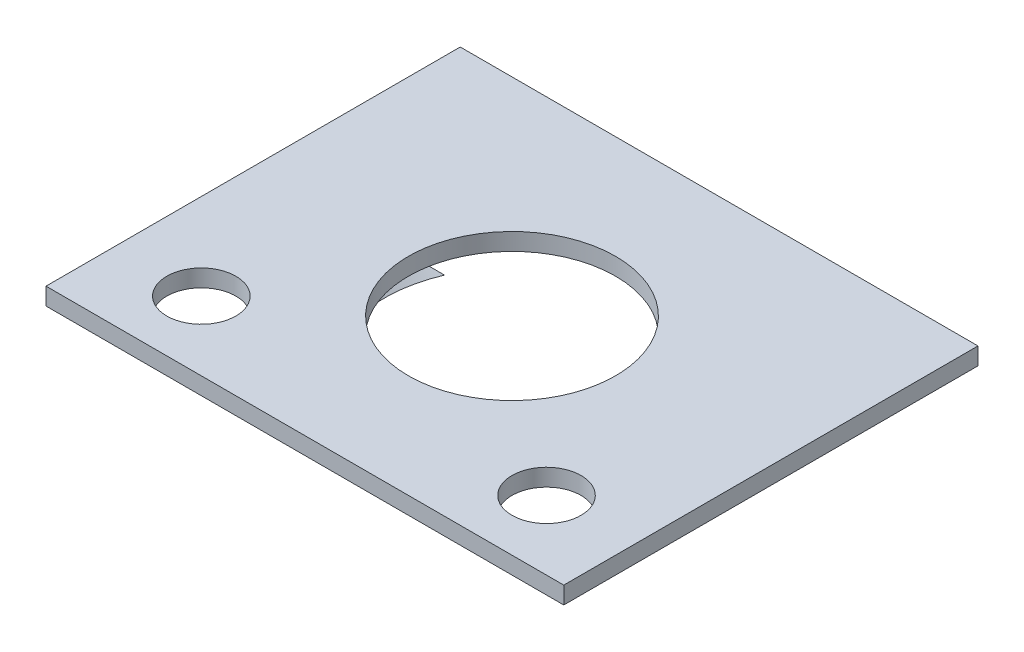
SolidWorks part; units mm, degrees
ref_plane "Front Plane" through (0, 0, 0) normal (0, 0, 1) x (1, 0, 0)
ref_plane "Top Plane" through (0, 0, 0) normal (0, 1, 0) x (1, 0, 0)
ref_plane "Right Plane" through (0, 0, 0) normal (1, 0, 0) x (0, 0, -1)
sketch "Sketch1" plane through (0, 0, 0) normal (0, 1, 0) x (1, 0, 0)
  line L0 (-19.05, 15.24) -> (19.05, -15.24) construction
  line L1 (-19.05, 15.24) -> (19.05, 15.24)
  line L2 (-19.05, 15.24) -> (-19.05, -15.24)
  line L3 (-19.05, -15.24) -> (19.05, -15.24)
  line L4 (19.05, 15.24) -> (19.05, -15.24)
  line L5 (19.05, 15.24) -> (-19.05, -15.24) construction
  line L6 (-12.7, -10.16) -> (12.7, -10.16) construction
  circle A0 centre (0, 0) radius 7.62
  circle A1 centre (12.7, -10.16) radius 2.54
  circle A2 centre (-12.7, -10.16) radius 2.54
  dimension "D3" = 15.24
  dimension "D4" = 5.08
  dimension "D1" = 38.1
  dimension "D2" = 30.48
  dimension "D5" = 5.08
extrude "Boss-Extrude1" add sketch "Sketch1" along normal blind 1.27
sketch "Sketch2" plane through (0, 0, 0) normal (0, -1, 0) x (-1, 0, 0)
  line L1 (-3.81, -10.6886) -> (0, -10.6886) construction
  line L2 (-3.81, -9.4186) -> (3.81, -9.4186)
  line L3 (-3.81, -9.4186) -> (-3.81, -11.9586)
  line L4 (-3.81, -11.9586) -> (3.81, -11.9586)
  line L5 (0, 15.24) -> (0, -15.24) construction
  line L6 (-19.05, 15.24) -> (19.05, 15.24) construction
  line L7 (3.81, -9.4186) -> (3.81, -11.9586)
  line L8 (0, -10.6886) -> (3.81, -10.6886) construction
  line L9 (9.7311, 2.921) -> (9.7311, -2.921) construction
  line L10 (-9.7311, 2.921) -> (-12.2711, 2.921)
  line L11 (-9.7311, 2.921) -> (-9.7311, -2.921) construction
  line L12 (-9.7311, -2.921) -> (-12.2711, -2.921)
  line L13 (-12.2711, 2.921) -> (-12.2711, -2.921)
  line L14 (9.7311, 2.921) -> (12.2711, 2.921)
  line L16 (9.7311, -2.921) -> (12.2711, -2.921)
  line L17 (12.2711, 2.921) -> (12.2711, -2.921)
  arc A0 (-9.7311, 2.921) -> (-9.7311, -2.921) centre (0, 0) ccw
  arc A1 (-3.81, -9.4186) -> (3.81, -9.4186) centre (0, 0) ccw
  arc A2 (9.7311, -2.921) -> (9.7311, 2.921) centre (0, 0) ccw
  dimension "D1" = 20.32
  dimension "D2" = 2.54
  dimension "D3" = 5.842
  dimension "D4" = 7.62
  dimension "D5" = 2.54
extrude "Boss-Extrude2" add sketch "Sketch2" along normal blind 1.524 contours A0 L10 L13 L12 | A1 L3 L4 L7 | A2 L16 L17 L14
sketch "Sketch4" plane through (0, -1.524, 0) normal (0, -1, 0) x (-1, 0, 0)
  line L2 (3.81, -9.4186) -> (3.81, -11.9586)
  line L3 (3.81, -11.9586) -> (-3.81, -11.9586)
  line L4 (-3.81, -9.4186) -> (-3.81, -11.9586)
  line L5 (12.2711, 2.921) -> (9.7311, 2.921)
  line L6 (12.2711, 2.921) -> (12.2711, -2.921)
  line L7 (12.2711, -2.921) -> (9.7311, -2.921)
  line L9 (-9.7311, 2.921) -> (-12.2711, 2.921)
  line L11 (-9.7311, -2.921) -> (-12.2711, -2.921)
  line L12 (-12.2711, 2.921) -> (-12.2711, -2.921)
  arc A0 (9.7311, -2.921) -> (9.7311, 2.921) centre (0, 0) ccw
  arc A1 (-3.81, -9.4186) -> (3.81, -9.4186) centre (0, 0) ccw construction
  arc A2 (-3.81, -9.4186) -> (3.81, -9.4186) centre (0, 0) ccw
  arc A3 (-9.7311, 2.921) -> (-9.7311, -2.921) centre (0, 0) ccw
extrude "Boss-Extrude3" add sketch "Sketch4" along normal blind 0.762 draft 45 draft outward yes
sketch "Sketch6" plane through (0, 0, 0) normal (0, -1, 0) x (-1, 0, 0)
  line L0 (2.54, -8.636) -> (-2.54, -7.62) construction
  line L1 (2.54, -8.636) -> (-2.54, -8.636)
  line L2 (2.54, -8.636) -> (2.54, -7.62)
  line L3 (2.54, -7.62) -> (-2.54, -7.62)
  line L4 (-2.54, -8.636) -> (-2.54, -7.62)
  line L5 (0, -8.636) -> (0, -7.62) construction
  line L6 (2.54, -10.16) -> (-2.54, -10.16)
  line L7 (2.54, -9.144) -> (-2.54, -9.144)
  line L8 (-2.54, -10.16) -> (-2.54, -9.144)
  line L9 (2.54, -10.16) -> (2.54, -9.144)
  circle A0 centre (0, 0) radius 7.62 construction
  dimension "D1" = 1.016
  dimension "D2" = 5.08
  dimension "D4" = 0.508
  dimension "D3" = 2
extrude "Boss-Extrude4" add sketch "Sketch6" along normal blind 0.254
